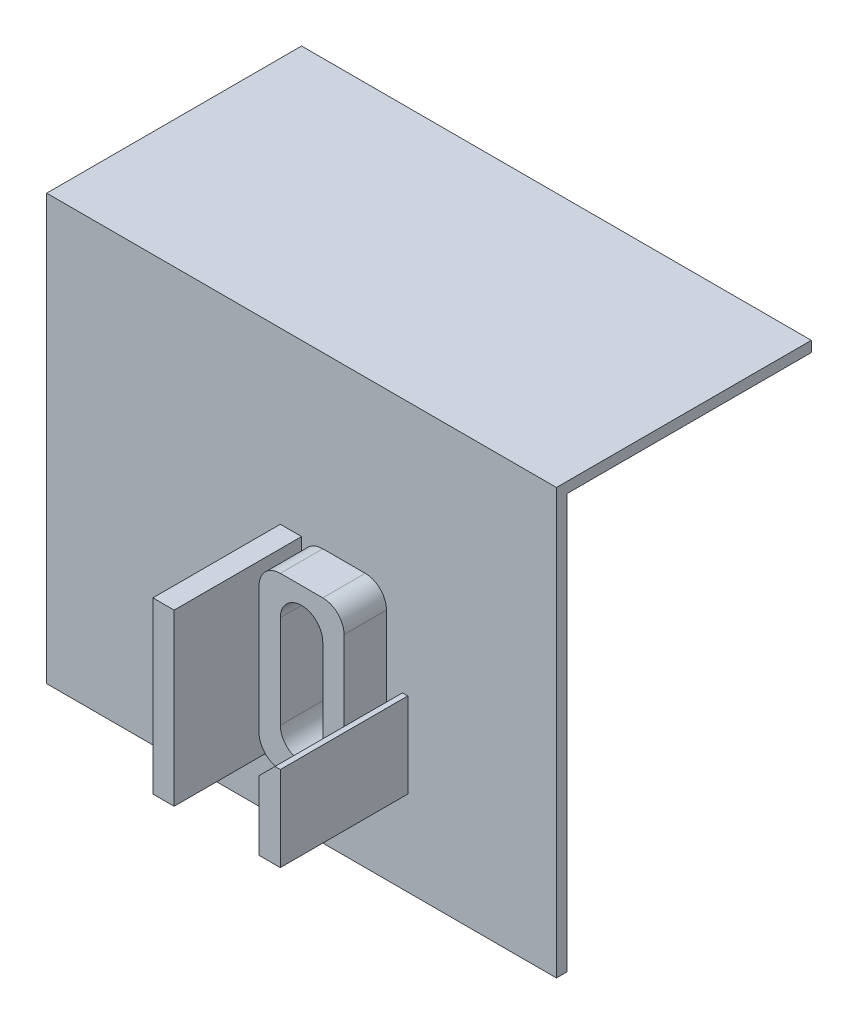
SolidWorks part; units mm, degrees
ref_plane "Front Plane" through (0, 0, 0) normal (0, 0, 1) x (1, 0, 0)
ref_plane "Top Plane" through (0, 0, 0) normal (0, 1, 0) x (1, 0, 0)
ref_plane "Right Plane" through (0, 0, 0) normal (1, 0, 0) x (0, 0, -1)
sketch "Sketch1" plane through (0, 0, 0) normal (1, 0, 0) x (0, 0, -1)
  line L0 (0, 0) -> (0, 63.5)
  line L1 (0, 63.5) -> (38.1, 63.5)
  line L2 (38.1, 63.5) -> (38.1, 61.9125)
  line L3 (38.1, 61.9125) -> (1.5875, 61.9125)
  line L4 (1.5875, 61.9125) -> (1.5875, 0)
  line L5 (1.5875, 0) -> (0, 0)
  dimension "D1" = 1.5875
  dimension "D2" = 1.5875
  dimension "D3" = 63.5
  dimension "D4" = 38.1
extrude "Boss-Extrude1" add sketch "Sketch1" along normal blind 76.2
sketch "Sketch2" plane through (0, 0, 0) normal (0, 0, 1) x (1, 0, 0)
  line L0 (41.275, 32.3582) -> (41.275, 18.4418)
  line L1 (41.275, 12.7) -> (47.625, 12.7)
  line L2 (38.1, 15.875) -> (38.1, 34.925)
  line L3 (41.275, 38.1) -> (47.625, 38.1)
  line L4 (50.8, 15.875) -> (50.8, 34.925)
  line L5 (47.625, 18.4418) -> (47.625, 32.3582)
  line L6 (0, 63.5) -> (0, 0) construction
  line L7 (76.2, 63.5) -> (0, 63.5) construction
  arc A2 (41.275, 32.3582) -> (47.625, 32.3582) centre (44.45, 32.3582) cw
  arc A3 (47.625, 18.4418) -> (41.275, 18.4418) centre (44.45, 18.4418) cw
  arc A4 (47.625, 12.7) -> (50.8, 15.875) centre (47.625, 15.875) ccw
  arc A5 (41.275, 12.7) -> (38.1, 15.875) centre (41.275, 15.875) cw
  arc A6 (47.625, 38.1) -> (50.8, 34.925) centre (47.625, 34.925) cw
  arc A7 (38.1, 34.925) -> (41.275, 38.1) centre (41.275, 34.925) cw
  point P10 (0, 0)
  point P11 (44.45, 38.1)
  point P12 (47.625, 25.4)
  point P13 (50.8, 25.4)
  point P20 (38.1, 12.7)
  point P23 (50.8, 38.1)
  point P26 (38.1, 38.1)
  dimension "D1" = 6.35
  dimension "D5" = 3.175
  dimension "D6" = 25.4
  dimension "D2" = 12.7
  dimension "D3" = 25.4
  dimension "D4" = 38.1
extrude "Boss-Extrude2" add sketch "Sketch2" along normal blind 6.35
sketch "Sketch3" plane through (0, 0, 0) normal (0, 0, 1) x (1, 0, 0)
  line L2 (47.625, 18.4418) -> (47.625, 32.3582)
  line L3 (41.275, 32.3582) -> (41.275, 18.4418)
  line L4 (47.625, 18.4418) -> (47.625, 32.3582)
  line L5 (41.275, 32.3582) -> (41.275, 18.4418)
  arc A2 (47.625, 32.3582) -> (41.275, 32.3582) centre (44.45, 32.3582) ccw
  arc A3 (41.275, 18.4418) -> (47.625, 18.4418) centre (44.45, 18.4418) ccw
  arc A4 (47.625, 32.3582) -> (41.275, 32.3582) centre (44.45, 32.3582) ccw
  arc A5 (41.275, 18.4418) -> (47.625, 18.4418) centre (44.45, 18.4418) ccw
  dimension "D1" = 0
extrude "Cut-Extrude1" cut sketch "Sketch3" against normal blind 6.35
sketch "Sketch4" plane through (0, 0, 0) normal (0, 0, 1) x (1, 0, 0)
  line L0 (50.8, 12.7) -> (50.8, 23.0188)
  line L1 (50.8, 15.875) -> (50.8, 34.925) construction
  line L2 (50.8, 23.0188) -> (53.1812, 25.4)
  line L3 (53.1812, 25.4) -> (53.975, 25.4)
  line L4 (53.975, 25.4) -> (53.975, 12.7)
  line L5 (53.975, 12.7) -> (50.8, 12.7)
  line L6 (41.275, 12.7) -> (47.625, 12.7) construction
  line L7 (41.275, 12.7) -> (47.625, 12.7) construction
  line L8 (38.1, 12.7) -> (34.925, 12.7)
  line L9 (38.1, 12.7) -> (38.1, 38.1)
  line L10 (38.1, 38.1) -> (34.925, 38.1)
  line L11 (34.925, 12.7) -> (34.925, 38.1)
  line L12 (47.625, 38.1) -> (41.275, 38.1) construction
  line L15 (38.1, 34.925) -> (38.1, 15.875) construction
  dimension "D1" = 12.7
  dimension "D2" = 3.175
  dimension "D3" = 0.7937
  dimension "D4" = 135
  dimension "D5" = 3.175
extrude "Boss-Extrude3" add sketch "Sketch4" along normal blind 19.05
